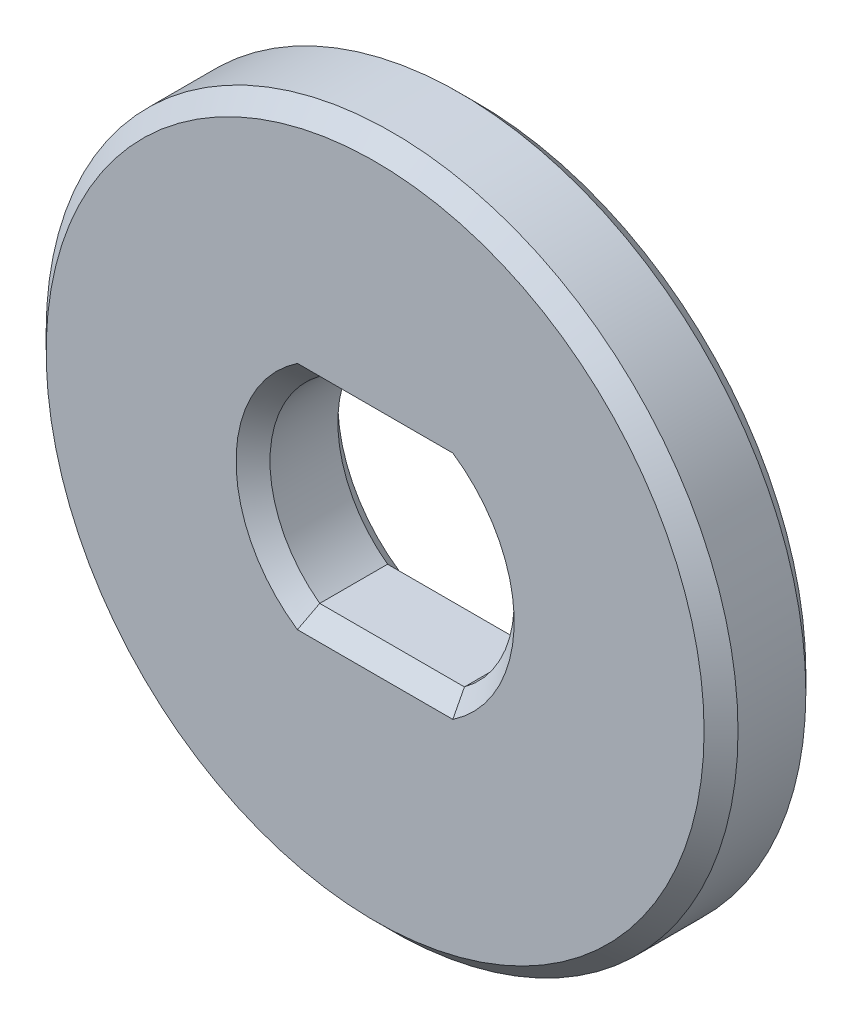
SolidWorks part; units mm, degrees
material "Polylactic Acid (PLA)"
ref_plane "Front Plane" through (0, 0, 0) normal (0, 0, 1) x (1, 0, 0)
ref_plane "Top Plane" through (0, 0, 0) normal (0, 1, 0) x (1, 0, 0)
ref_plane "Right Plane" through (0, 0, 0) normal (1, 0, 0) x (0, 0, -1)
sketch "Sketch1" plane through (0, 0, 0) normal (0, 0, 1) x (1, 0, 0)
  line L0 (-2.1331, 2.9) -> (2.1331, 2.9)
  line L1 (-1.9975, -2.5) -> (1.9975, -2.5) construction
  line L2 (-1.9975, -2.5) -> (-1.9975, 2.5) construction
  line L3 (-1.9975, 2.5) -> (1.9975, 2.5) construction
  line L4 (1.9975, -2.5) -> (1.9975, 2.5) construction
  line L5 (-1.9975, -2.5) -> (1.9975, 2.5) construction
  line L6 (-1.9975, 2.5) -> (1.9975, -2.5) construction
  line L7 (-2.1331, -2.9) -> (2.1331, -2.9)
  circle A0 centre (0, 0) radius 10.2
  arc A1 (-1.9975, 2.5) -> (-1.9975, -2.5) centre (0, 0) ccw construction
  arc A2 (1.9975, -2.5) -> (1.9975, 2.5) centre (0, 0) ccw construction
  arc A3 (2.1331, -2.9) -> (2.1331, 2.9) centre (0, 0) ccw
  arc A4 (-2.1331, 2.9) -> (-2.1331, -2.9) centre (0, 0) ccw
  dimension "D1" = 20.4
  dimension "D2" = 6.4
  dimension "D3" = 2.5
  dimension "D4" = 0.4
extrude "Boss-Extrude1" add sketch "Sketch1" along normal blind 3
chamfer "Chamfer1" distance 0.5 angle 45 10 edges at (3.6, 0, 0) (0, -2.9, 0) (0, 2.9, 0) (-3.6, 0, 0) (10.2, 0, 0) (0, 2.9, 3) (-3.6, 0, 3) (3.6, 0, 3) (0, -2.9, 3) (10.2, 0, 3)
